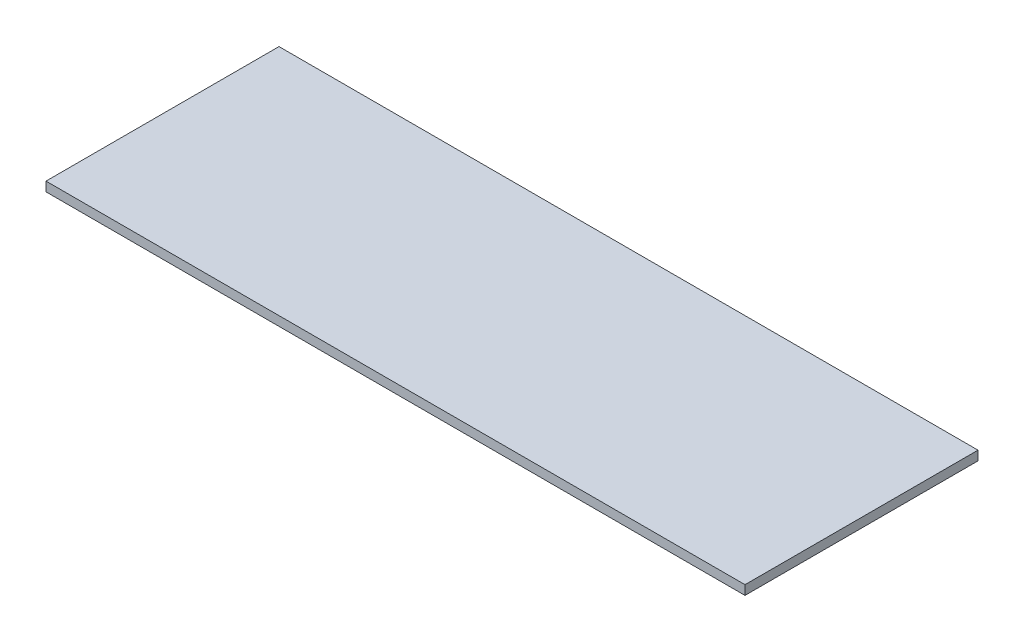
SolidWorks part; units mm, degrees
ref_plane "Front Plane" through (0, 0, 0) normal (0, 0, 1) x (1, 0, 0)
ref_plane "Top Plane" through (0, 0, 0) normal (0, 1, 0) x (1, 0, 0)
ref_plane "Right Plane" through (0, 0, 0) normal (1, 0, 0) x (0, 0, -1)
sketch "Sketch1" plane through (0, 0, 0) normal (0, 1, 0) x (1, 0, 0)
  line L1 (0, 0) -> (75, 0)
  line L2 (0, 0) -> (0, 25)
  line L3 (0, 25) -> (75, 25)
  line L4 (75, 0) -> (75, 25)
  dimension "D1" = 75
  dimension "D2" = 25
extrude "Boss-Extrude1" add sketch "Sketch1" along normal blind 1
sketch "Sketch2" plane through (0, 1, 0) normal (0, 1, 0) x (1, 0, 0)
  line L0 (0, 0) -> (75, 25) construction
  circle A0 centre (37.5, 12.5) radius 6 construction
  dimension "D1" = 12
